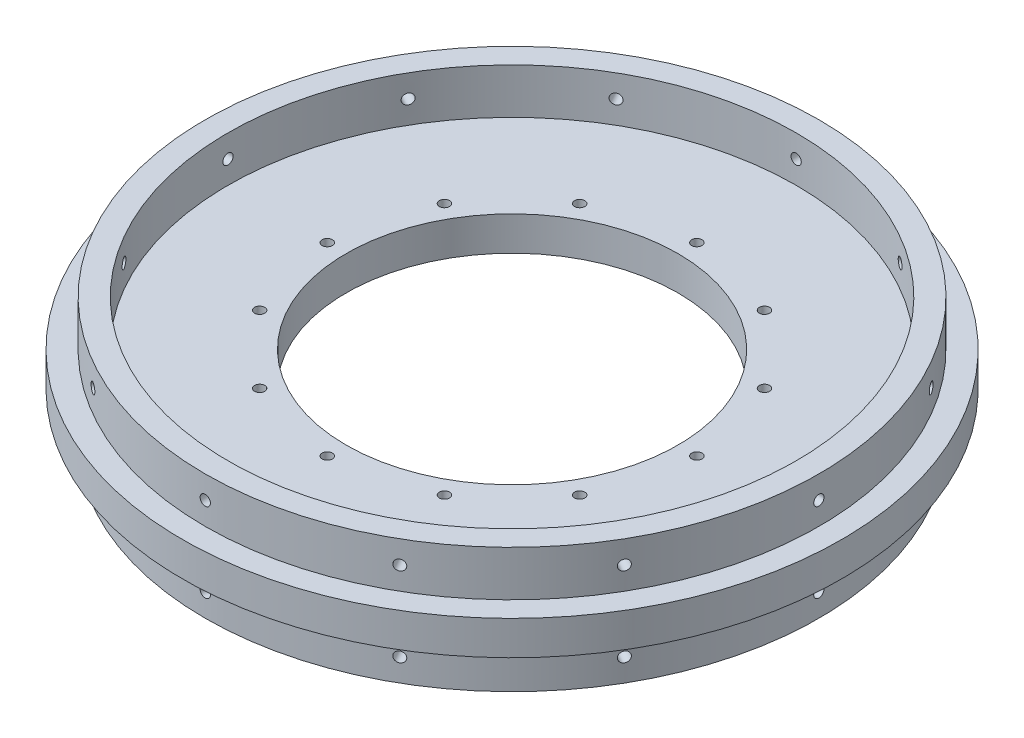
SolidWorks part; units mm, degrees
material "6061-T6 (SS)"
ref_plane "Front Plane" through (0, 0, 0) normal (0, 0, 1) x (1, 0, 0)
ref_plane "Top Plane" through (0, 0, 0) normal (0, 1, 0) x (1, 0, 0)
ref_plane "Right Plane" through (0, 0, 0) normal (1, 0, 0) x (0, 0, -1)
sketch "Sketch1" plane through (0, 0, 0) normal (0, 1, 0) x (1, 0, 0)
  line L5 (0, 0) -> (127.635, 0)
  line L6 (0, 0) -> (0, 127.635)
  line L7 (0, 127.635) -> (127.635, 127.635)
  line L8 (127.635, 0) -> (127.635, 127.635)
  dimension "D1" = 127.635
  dimension "D2" = 127.635
extrude "Boss-Extrude1" add sketch "Sketch1" along normal blind 9.525 contours L5 L8 L7 L6
sketch "Sketch12" plane through (0, 0, 0) normal (0, -1, 0) x (1, 0, 0)
  line L0 (63.8175, 0) -> (63.8175, -127.635) construction
  line L1 (0, 0) -> (127.635, 0) construction
  line L2 (0, -127.635) -> (127.635, -127.635) construction
  line L3 (0, -63.8175) -> (127.635, -63.8175) construction
  line L4 (0, 0) -> (0, -127.635) construction
  line L5 (127.635, 0) -> (127.635, -127.635) construction
  circle A0 centre (63.8175, -63.8175) radius 92.075
  dimension "D1" = 184.15
extrude "Boss-Extrude2" add sketch "Sketch12" against normal up to surface (9.525 mm away) contours A0 up to face at (63.8175, 9.525, -63.8175)
sketch "Sketch5" plane through (0, 9.525, 0) normal (0, 1, 0) x (1, 0, 0)
  circle A0 centre (63.8175, 63.8175) radius 46.355
  circle A3 centre (63.8175, 63.8175) radius 92.075 construction
  dimension "D1" = 92.71
extrude "Cut-Extrude1" cut sketch "Sketch5" against normal blind 9.525
sketch "Sketch11" plane through (0, 9.525, 0) normal (0, 1, 0) x (1, 0, 0)
  line L0 (63.8175, 63.8175) -> (63.8175, 115.443) construction
  circle A0 centre (63.8175, 115.443) radius 1.4351
  dimension "D2" = 2.8702
  dimension "D1" = 51.6255
extrude "Cut-Extrude3" cut sketch "Sketch11" against normal through all contours A0
pattern_circular "CirPattern1" count 12 over 360 about axis through (63.8175, 0, -63.8175) along (0, 1, 0) of "Cut-Extrude3"
sketch "Sketch14" plane through (0, 9.525, 0) normal (0, -1, 0) x (1, 0, 0)
  line L0 (63.8175, -63.8175) -> (147.6375, -63.8175) construction
  line L1 (0, -5.2388) -> (0, 5.2388) construction
  line L2 (147.6375, -63.8175) -> (152.7175, -63.8175)
  line L3 (136.3808, -105.7742) -> (140.8401, -108.2104)
  circle A0 centre (63.8175, -63.8175) radius 46.355 construction
  arc A2 (147.6375, -63.8175) -> (136.3808, -105.7742) centre (63.8175, -63.8175) cw
  arc A3 (152.7175, -63.8175) -> (140.8401, -108.2104) centre (63.8175, -63.8175) cw
  point P0 (63.8175, -63.8175)
  dimension "D1" = 83.82
  dimension "D2" = 88.9
  dimension "D3" = 46.482
  dimension "D4" = 43.942
ref_plane "Support mirror reference plane" through (0, 4.7625, 0) normal (0, 1, 0) x (1, 0, 0)
sketch "Sketch25" plane through (0, 9.525, 0) normal (0, -1, 0) x (1, 0, 0)
  line L0 (63.8175, -63.8175) -> (123.0872, -4.5478) construction
  line L2 (123.0872, -4.5478) -> (126.6793, -0.9557)
  line L3 (144.7953, -42.1754) -> (149.6712, -40.7448)
  line L5 (63.8175, -63.8175) -> (147.6375, -63.8175) construction
  arc A2 (123.0872, -4.5478) -> (144.7953, -42.1754) centre (63.8175, -63.8175) cw
  arc A3 (126.6793, -0.9557) -> (149.6712, -40.7448) centre (63.8175, -63.8175) cw
  point P0 (63.8175, -63.8175)
  dimension "D1" = 83.82
  dimension "D2" = 88.9
  dimension "D3" = 46.482
  dimension "D4" = 43.942
  dimension "D5" = 45
sketch "Sketch30" plane through (0, 0, 0) normal (0, -1, 0) x (1, 0, 0)
  circle A0 centre (63.8175, -63.8175) radius 85.725
  circle A1 centre (63.8175, -63.8175) radius 79.375
  dimension "D1" = 171.45
  dimension "D2" = 158.75
extrude "Boss-Extrude3" add sketch "Sketch30" along normal blind 12.7
mirror "Mirror1" about plane through (0, 4.7625, 0) normal (0, 1, 0) of "Boss-Extrude3"
sketch "Sketch31" plane through (0, 0, 0) normal (0, -1, 0) x (-1, 0, 0)
  line L0 (-63.8175, -52.481) -> (-63.8175, 177.7216) construction
ref_plane "Plane1" through (0, 0, -149.5425) normal (0, 0, -1) x (-1, 0, 0)
ref_plane "Plane2" through (63.8175, 0, 0) normal (-1, 0, 0) x (0, 0, -1)
sketch "Sketch32" plane through (0, 0, -149.5425) normal (0, 0, -1) x (-1, 0, 0)
  line L4 (-63.8175, -87.3125) -> (-63.8175, 87.3125) construction
  line L5 (-149.5425, 0) -> (21.9075, 0) construction
  line L6 (21.9075, 9.525) -> (-149.5425, 9.525) construction
  circle A0 centre (-63.8175, -6.35) radius 1.4351
  circle A1 centre (-63.8175, 15.875) radius 1.4351
  dimension "D1" = 2.8702
  dimension "D2" = 2.8702
  dimension "D3" = 6.35
  dimension "D4" = 6.35
extrude "Cut-Extrude4" cut sketch "Sketch32" against normal blind 15.24
pattern_circular "CirPattern2" count 12 over 360 about axis through (63.8175, -12.7, -63.8175) along (0, 1, 0) of "Cut-Extrude4"
